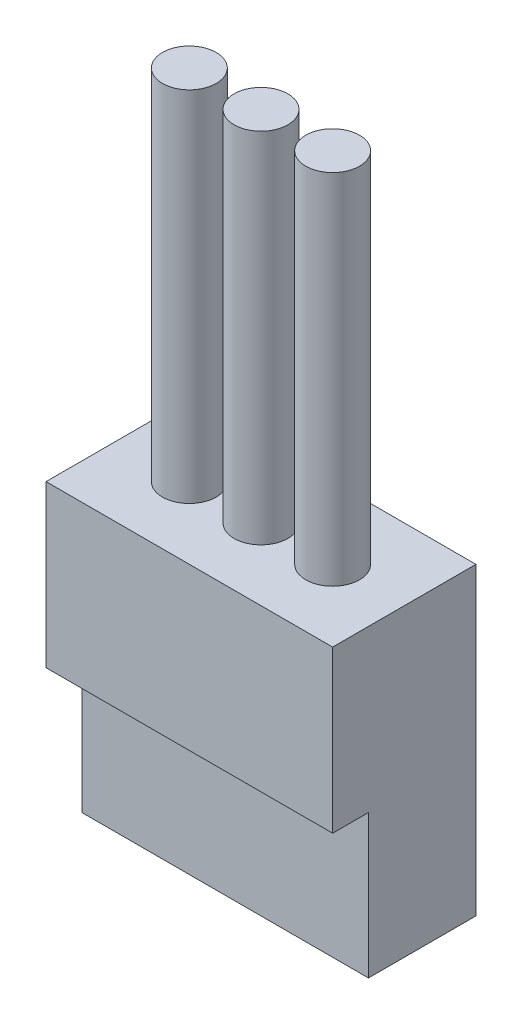
SolidWorks part; units mm, degrees
ref_plane "Face" through (0, 0, 0) normal (0, 0, 1) x (1, 0, 0)
ref_plane "Dessus" through (0, 0, 0) normal (0, 1, 0) x (1, 0, 0)
ref_plane "Droite" through (0, 0, 0) normal (1, 0, 0) x (0, 0, -1)
sketch "Esquisse1" plane through (0, 0, 0) normal (0, 1, 0) x (1, 0, 0)
  line L0 (0, 0) -> (8, 0)
  line L1 (8, 0) -> (8, -3)
  line L2 (8, -3) -> (0, -3)
  line L3 (0, -3) -> (0, 0)
  dimension "D1" = 3
  dimension "D2" = 8
extrude "Extrusion1" add sketch "Esquisse1" along normal blind 4
sketch "Esquisse2" plane through (0, 4, 0) normal (0, 1, 0) x (1, 0, 0)
  line L0 (8, -3) -> (8, 0) construction
  line L1 (0, 0) -> (8, 0)
  line L2 (0, 0) -> (0, -4)
  line L3 (0, -4) -> (8, -4)
  line L4 (8, 0) -> (8, -4)
  dimension "D1" = 4
extrude "Extrusion2" add sketch "Esquisse2" along normal blind 4.5
sketch "Esquisse3" plane through (0, 8.5, 0) normal (0, 1, 0) x (1, 0, 0)
  line L0 (0, -2) -> (8, -2) construction
  line L1 (0, 0) -> (0, -4) construction
  line L2 (8, -4) -> (8, 0) construction
  line L3 (4, 0) -> (4, -4) construction
  line L4 (8, 0) -> (0, 0) construction
  line L5 (0, -4) -> (8, -4) construction
  circle A0 centre (4, -2) radius 0.75
  circle A1 centre (2, -2) radius 0.75
  circle A2 centre (6, -2) radius 0.75
  dimension "D1" = 1.5
  dimension "D2" = 2
extrude "Extrusion3" add sketch "Esquisse3" along normal blind 10
